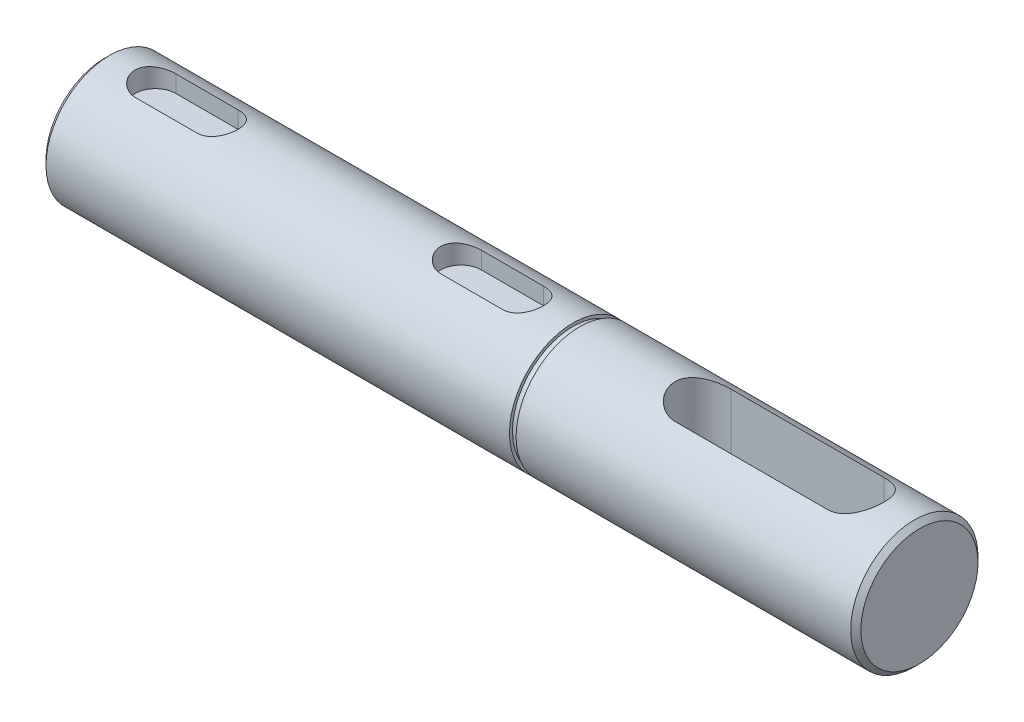
SolidWorks part; units mm, degrees
material "AISI 304"
ref_plane "Спереди" through (0, 0, 0) normal (0, 0, 1) x (1, 0, 0)
ref_plane "Сверху" through (0, 0, 0) normal (0, 1, 0) x (1, 0, 0)
ref_plane "Справа" through (0, 0, 0) normal (1, 0, 0) x (0, 0, -1)
sketch "Эскиз1" plane through (0, 0, 0) normal (1, 0, 0) x (0, 0, -1)
  circle A0 centre (0, 0) radius 15
  dimension "D1" = 30
extrude "Бобышка-Вытянуть1" add sketch "Эскиз1" along normal blind 160
sketch "Эскиз2" plane through (0, 0, 0) normal (-1, 0, 0) x (0, 0, 1)
  circle A0 centre (0, 0) radius 12.5
  dimension "D1" = 25
extrude "Вырез-Вытянуть1" cut sketch "Эскиз2" against normal blind 92 flip side to cut
sketch "Эскиз3" plane through (160, 0, 0) normal (1, 0, 0) x (0, 0, -1)
  circle A0 centre (0, 0) radius 12.5
  dimension "D1" = 25
extrude "Вырез-Вытянуть2" cut sketch "Эскиз3" against normal offset from surface (63 mm away) 5 flip side to cut up to face at (92, 0, 12.5)
chamfer "Фаска1" distance 1 angle 45 4 edges at (92, 0, 15) (97, 0, 15) (0, 0, 12.5) (160, 0, -12.5)
sketch "Эскиз4" plane through (0, 0, 0) normal (0, 1, 0) x (1, 0, 0)
  line L0 (0, 0) -> (71.8511, 0) construction
  line L1 (10, 0) -> (22.2, 0) construction
  line L2 (10, 4) -> (22.2, 4)
  line L3 (10, -4) -> (22.2, -4)
  line L4 (70, 0) -> (82.2, 0) construction
  line L5 (70, 4) -> (82.2, 4)
  line L6 (70, -4) -> (82.2, -4)
  line L7 (0, 11.5) -> (0, -11.5) construction
  arc A0 (10, 4) -> (10, -4) centre (10, 0) ccw
  arc A1 (22.2, -4) -> (22.2, 4) centre (22.2, 0) ccw
  arc A2 (70, 4) -> (70, -4) centre (70, 0) ccw
  arc A3 (82.2, -4) -> (82.2, 4) centre (82.2, 0) ccw
  point P5 (16.1, 0)
  point P10 (76.1, 0)
  dimension "D1" = 8
  dimension "D2" = 12.2
  dimension "D3" = 10
  dimension "D4" = 60
extrude "Вырез-Вытянуть3" cut sketch "Эскиз4" against normal blind 4 from offset 12.5
hole_wizard "Отверстие обработанное метчиком M121" positions "Эскиз6" profile "Эскиз5" tap size "M12" standard "DIN"
sketch "Эскиз6" plane through (0, 0, 0) normal (-1, 0, 0) x (0, 0, 1)
  point P0 (0, 0)
sketch "Эскиз5" plane through (0, 0, 0) normal (0, 1, 0) x (0, 0, 1)
  line L0 (0, 0) -> (0, 35.6945)
  line L1 (0, 35.6945) -> (5.1, 32.75)
  line L2 (5.1, 32.75) -> (5.1, 0)
  line L5 (5.1, 0) -> (0, 0)
  line L10 (0, 35.6945) -> (-5.1, 32.75) construction
  line L11 (0, -6.35) -> (0, 107.95) construction
  dimension "Диаметр сверла" = 10.2
  dimension "Глубина сверла" = 32.75
  dimension "Угол заточки сверла" = 120
cosmetic thread "Отверстие резьбы1" parameters "D1"=24, "D2"=12
chamfer "Фаска2" distance 1 angle 45 1 edges at (0, 0, 5.1)
sketch "Эскиз8" plane through (0, 0, 0) normal (0, 1, 0) x (1, 0, 0)
  line L0 (160, 0) -> (147.5, 0) construction
  line L1 (160, -11.5) -> (160, 11.5) construction
  line L2 (147.5, 0) -> (117.5, 0) construction
  line L3 (147.5, -5.5) -> (117.5, -5.5)
  line L4 (147.5, 5.5) -> (117.5, 5.5)
  circle A0 centre (147.5, 0) radius 5.5 construction
  arc A1 (147.5, -5.5) -> (147.5, 5.5) centre (147.5, 0) ccw
  arc A2 (117.5, 5.5) -> (117.5, -5.5) centre (117.5, 0) ccw
  point P6 (132.5, 0)
  dimension "D1" = 11
  dimension "D2" = 12.5
  dimension "D3" = 11
  dimension "D4" = 30
extrude "Вырез-Вытянуть4" cut sketch "Эскиз8" against normal through all both and the other way through all
sketch "Эскиз9" plane through (92, 0, 0) normal (-1, 0, 0) x (0, 0, 1)
  circle A0 centre (0, 0) radius 11.9
  circle A1 centre (0, 0) radius 15
  circle A2 centre (0, 0) radius 15 construction
  dimension "D1" = 23.8
extrude "Вырез-Вытянуть5" cut sketch "Эскиз9" against normal blind 1.3
sketch "Эскиз10" plane through (97, 0, 0) normal (1, 0, 0) x (0, 0, -1)
  circle A0 centre (0, 0) radius 12.5 construction
  circle A1 centre (0, 0) radius 15 construction
  circle A2 centre (0, 0) radius 12.5
  circle A3 centre (0, 0) radius 15
extrude "Вырез-Вытянуть6" cut sketch "Эскиз10" against normal blind 7.3
